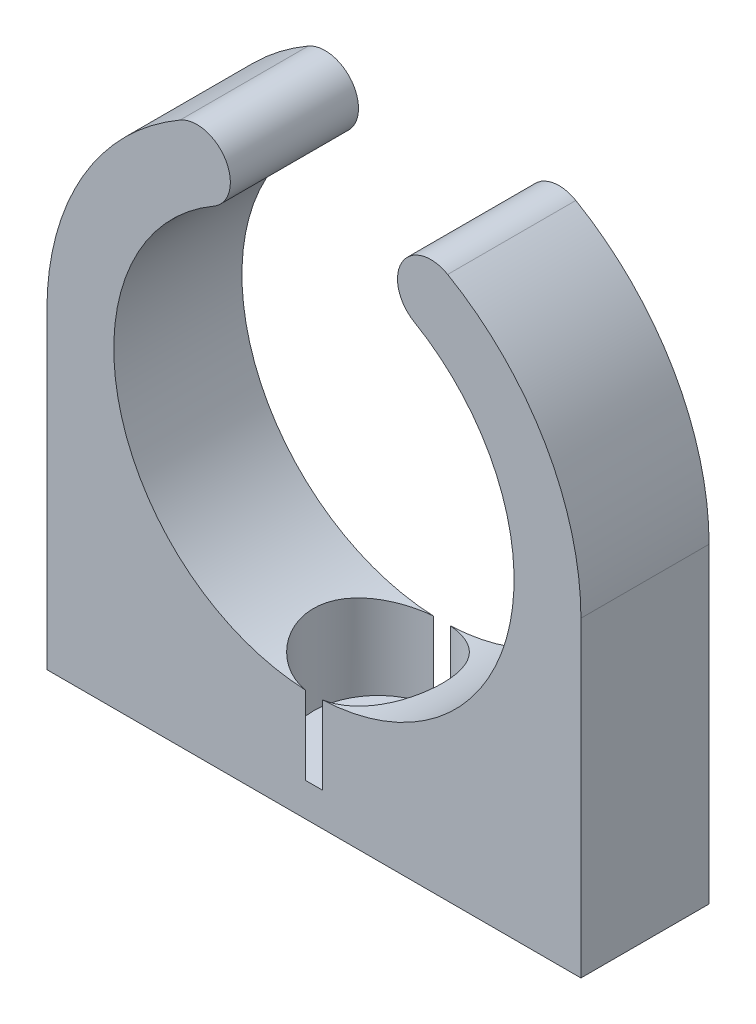
SolidWorks part; units mm, degrees
material "ABS"
ref_plane "Front Plane" through (0, 0, 0) normal (0, 0, 1) x (1, 0, 0)
ref_plane "Top Plane" through (0, 0, 0) normal (0, 1, 0) x (1, 0, 0)
ref_plane "Right Plane" through (0, 0, 0) normal (1, 0, 0) x (0, 0, -1)
sketch "Sketch1" plane through (0, 0, 0) normal (0, 0, 1) x (1, 0, 0)
  line L0 (-11.98, -13.98) -> (11.98, -13.98)
  line L1 (11.98, -13.98) -> (11.98, 0)
  line L2 (-11.98, -13.98) -> (-11.98, 0)
  circle A0 centre (0, 0) radius 9 construction
  arc A1 (-8.98, 0) -> (4.4986, 7.772) centre (0, 0) ccw
  arc A2 (11.98, 0) -> (6.0014, 10.3684) centre (0, 0) ccw
  arc A3 (-4.4986, 7.772) -> (-6.0014, 10.3684) centre (-5.25, 9.0702) ccw
  circle A4 centre (0, 0) radius 11.98 construction
  circle A5 centre (0, 0) radius 8.98 construction
  arc A6 (6.0014, 10.3684) -> (4.4986, 7.772) centre (5.25, 9.0702) ccw
  arc A7 (-4.4986, 7.772) -> (-8.98, 0) centre (0, 0) ccw
  arc A8 (-6.0014, 10.3684) -> (-11.98, 0) centre (0, 0) ccw
  point P10 (0, -13.98)
  point P17 (13.4074, 4.0991)
  point P22 (8.6259, 2.6372)
  dimension "D1" = 18
  dimension "D7" = 7.5
  dimension "D4" = 5
  dimension "D3" = 3
extrude "Boss-Extrude1" add sketch "Sketch1" along normal mid plane 5.75 contours L1 A2 L2 L0 A1
sketch "Sketch4" plane through (0, 0, 0) normal (0, 0, 1) x (1, 0, 0)
  line L0 (1.5, -12.48) -> (2.9, -12.48)
  line L1 (-2.9, -7.48) -> (2.9, -7.48)
  line L2 (-2.9, -7.48) -> (-2.9, -12.48)
  line L3 (-2.9, -12.48) -> (-1.5, -12.48)
  line L4 (2.9, -7.48) -> (2.9, -12.48)
  line L5 (-2.9, -7.48) -> (2.9, -12.48) construction
  line L6 (-2.9, -12.48) -> (2.9, -7.48) construction
  line L8 (-1.5, -12.48) -> (-1.5, -13.98)
  line L9 (-1.5, -13.98) -> (1.5, -13.98)
  line L10 (1.5, -12.48) -> (1.5, -13.98)
  line L11 (-1.5, -12.48) -> (1.5, -13.98) construction
  line L12 (-1.5, -13.98) -> (1.5, -12.48) construction
  line L13 (-11.98, -13.98) -> (11.98, -13.98) construction
  line L14 (0, -13.98) -> (0, -7.48)
  arc A2 (-4.4986, 7.772) -> (4.4986, 7.772) centre (0, 0) ccw construction
  point P0 (0, -9.98)
  point P5 (0, -13.23)
  dimension "D3" = 3
  dimension "D1" = 5.8
  dimension "D4" = 3.5
  dimension "D2" = 5
revolve "Cut-Revolve1" cut sketch "Sketch4" angle 360 about L14
equation "\"diam\"= 18mm"
equation "\"width\"= 5.75"
equation "\"D1@Sketch1\"=\"diam\""
equation "\"tolerance\"= 0.02"
equation "\"D2@Sketch1\"=\"tolerance\""
equation "\"D1@Boss-Extrude1\"=\"width\""
equation "\"bolt_outer diam\"= 5.8mm"
equation "\"bolt diam\"= 3"
equation "\"bolt head thickness\"= 3.5"
equation "\"D1@Sketch4\"=\"bolt_outer diam\""
equation "\"D3@Sketch4\"=\"bolt diam\""
equation "\"D4@Sketch4\"=\"bolt head thickness\""
